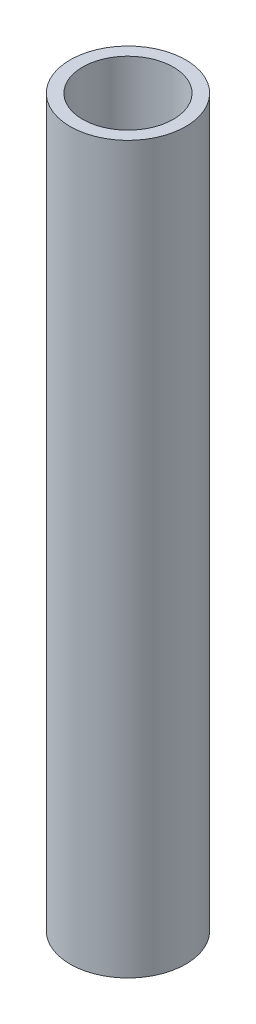
SolidWorks part; units mm, degrees
material "PVC Rigid"
ref_plane "Front Plane" through (0, 0, 0) normal (0, 0, 1) x (1, 0, 0)
ref_plane "Top Plane" through (0, 0, 0) normal (0, 1, 0) x (1, 0, 0)
ref_plane "Right Plane" through (0, 0, 0) normal (1, 0, 0) x (0, 0, -1)
sketch "Sketch1" plane through (0, 0, 0) normal (0, 1, 0) x (1, 0, 0)
  circle A0 centre (0, 0) radius 24.2824
  circle A1 centre (0, 0) radius 19.05
  dimension "D1" = 48.5648
  dimension "D2" = 38.1
extrude "Boss-Extrude1" add sketch "Sketch1" along normal mid plane 304.8
